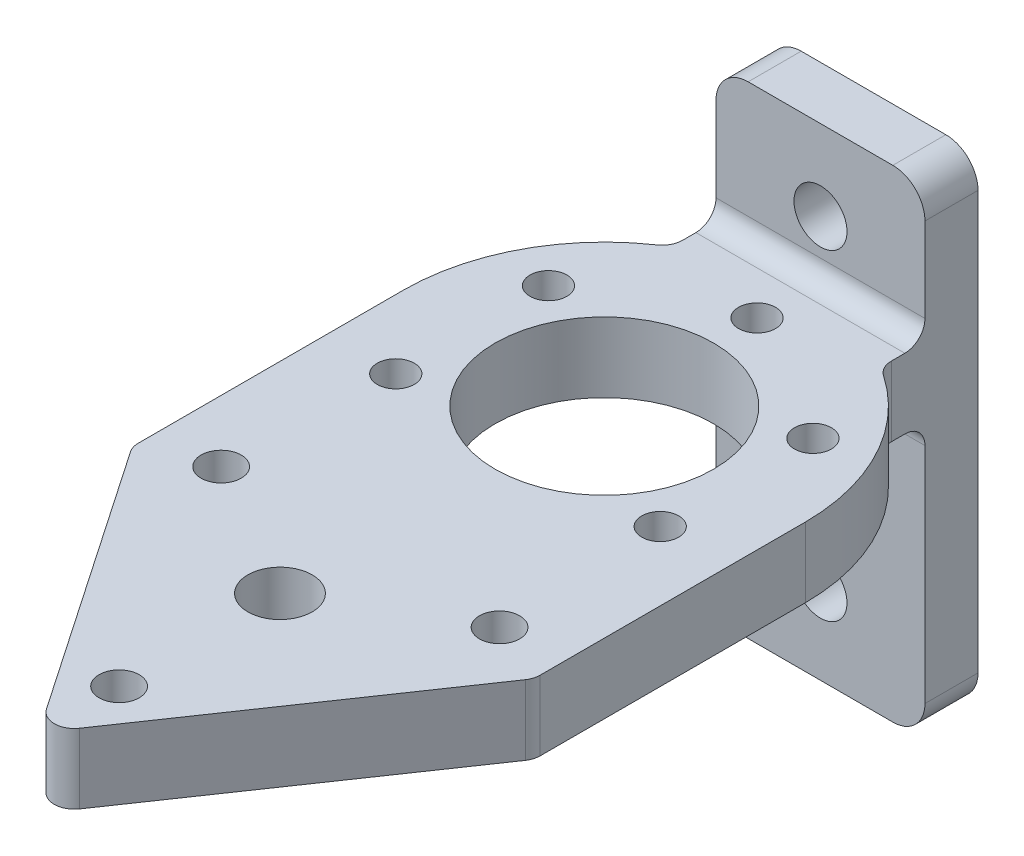
SolidWorks part; units mm, degrees
material "PLA"
ref_plane "Plan de face" through (0, 0, 0) normal (0, 0, 1) x (1, 0, 0)
ref_plane "Plan de dessus" through (0, 0, 0) normal (0, 1, 0) x (1, 0, 0)
ref_plane "Plan de droite" through (0, 0, 0) normal (1, 0, 0) x (0, 0, -1)
sketch "Esquisse1" plane through (0, 0, 0) normal (0, 0, 1) x (1, 0, 0)
  line L0 (55, 0) -> (-55, 0) construction
  line L1 (-6.5, -15) -> (6.5, -15)
  line L2 (-6.5, -15) -> (-6.5, 15)
  line L3 (-6.5, 15) -> (6.5, 15)
  line L4 (6.5, -15) -> (6.5, 15)
  line L5 (-6.5, -15) -> (6.5, 15) construction
  line L6 (-6.5, 15) -> (6.5, -15) construction
  circle A0 centre (0, 10) radius 1.65
  circle A1 centre (0, -10) radius 1.65
  point P0 (0, 0)
  dimension "D4" = 3.3
  dimension "D1" = 30
  dimension "D2" = 13
  dimension "D3" = 10
extrude "Boss.-Extru.1" add sketch "Esquisse1" along normal blind 3.3
fillet "Congé1" radius 2 4 edges at (6.5, -15, 1.65) (-6.5, -15, 1.65) (6.5, 15, 1.65) (-6.5, 15, 1.65)
sketch "Esquisse2" plane through (0, 0, 3.3) normal (0, 0, 1) x (1, 0, 0)
  line L0 (6.5, -13) -> (6.5, 13) construction
  line L3 (-6.5, 6.5) -> (6.5, 6.5)
  line L5 (-6.5, 13) -> (-6.5, -13) construction
  line L7 (-6.5, 6.5) -> (-6.5, 2.15)
  line L10 (-6.5, 2.15) -> (6.5, 2.15)
  line L14 (6.5, 6.5) -> (6.5, 2.15)
  point P0 (0, 0)
  point P8 (0, 0)
  dimension "D1" = 2.15
  dimension "D3" = 4.35
extrude "Boss.-Extru.2" add sketch "Esquisse2" along normal blind 2.77
sketch "Esquisse4" plane through (0, 6.5, 0) normal (0, 1, 0) x (1, 0, 0)
  line L1 (-6.5, -6.07) -> (6.5, -6.07)
  line L3 (-6.5, -27.4242) -> (6.5, -27.4242)
  circle A4 centre (0, -16.7471) radius 6.8
  arc A5 (-6.5, -6.07) -> (-6.5, -27.4242) centre (0, -16.7471) ccw
  arc A6 (6.5, -27.4242) -> (6.5, -6.07) centre (0, -16.7471) ccw
  point P25 (0, -16.7471)
  point P28 (0, -16.7471)
  dimension "D2" = 12.5
  dimension "D3" = 13
  dimension "D6" = 13.6
  dimension "D1" = 12.5
extrude "Boss.-Extru.4" add sketch "Esquisse4" against normal up to surface (4.35 mm away) up to face at (0, 2.15, 4.685)
sketch "Esquisse6" plane through (0, 6.5, 0) normal (0, 1, 0) x (1, 0, 0)
  line L2 (0, -16.7471) -> (8.2272, -11.9971) construction
  line L3 (0, -16.7471) -> (-8.2272, -11.9971) construction
  line L4 (0, -16.7471) -> (0, -7.2471) construction
  line L5 (0, -16.7471) -> (-8.2272, -21.4971) construction
  line L6 (0, -16.7471) -> (0, -26.2471) construction
  line L7 (0, -16.7471) -> (8.2272, -21.4971) construction
  circle A0 centre (0, -7.2471) radius 1.15
  circle A1 centre (-8.2272, -11.9971) radius 1.15
  circle A2 centre (8.2272, -11.9971) radius 1.15
  circle A3 centre (-8.2272, -21.4971) radius 1.15
  circle A7 centre (8.2272, -21.4971) radius 1.15
  dimension "D2" = 2.3
  dimension "D5" = 2.3
  dimension "D6" = 2.3
  dimension "D7" = 9.5
  dimension "D14" = 2.3
  dimension "D15" = 2.3
  dimension "D1" = 9.5
  dimension "D3" = 60
  dimension "D4" = 60
  dimension "D8" = 9.5
  dimension "D9" = 60
  dimension "D10" = 60
  dimension "D11" = 9.5
  dimension "D12" = 9.5
  dimension "D13" = 9.5
extrude "Enlèv. mat.-Extru.2" cut sketch "Esquisse6" against normal through all
sketch "Esquisse8" plane through (0, 6.5, 0) normal (0, 1, 0) x (1, 0, 0)
  line L6 (-6.5, -27.4242) -> (6.5, -27.4242) construction
  line L8 (0, -9.9471) -> (0, -23.5471) construction
  line L9 (0, -36.9271) -> (0, -27.4242) construction
  line L10 (0, -36.9271) -> (8.6603, -31.9271) construction
  line L11 (0, -36.9271) -> (-8.6603, -31.9271) construction
  line L16 (12.5, -16.7471) -> (12.5, -33.6271) construction
  line L17 (-12.5, -16.7471) -> (-12.5, -33.6258) construction
  line L18 (0, -51.9371) -> (-12.5, -33.6258)
  line L19 (-12.5, -33.6258) -> (-12.5, -16.7471)
  line L20 (0, -51.9371) -> (12.5, -33.6271)
  line L21 (12.5, -33.6271) -> (12.5, -16.7471)
  line L22 (-6.5, -27.4242) -> (6.5, -27.4242)
  circle A0 centre (0, -36.9271) radius 2
  circle A1 centre (0, -36.9271) radius 10 construction
  circle A2 centre (8.6603, -31.9271) radius 1.25
  circle A3 centre (0, -16.7471) radius 6.8 construction
  circle A4 centre (-8.6603, -31.9271) radius 1.25
  circle A7 centre (0, -46.9371) radius 1.25
  arc A8 (6.5, -27.4242) -> (6.5, -6.07) centre (0, -16.7471) ccw construction
  arc A9 (-6.5, -6.07) -> (-6.5, -27.4242) centre (0, -16.7471) ccw construction
  arc A11 (-12.5, -16.7471) -> (-6.5, -27.4242) centre (0, -16.7471) ccw
  arc A12 (12.5, -16.7471) -> (6.5, -27.4242) centre (0, -16.7471) cw
  point P16 (0, -16.7471)
  dimension "D2" = 4
  dimension "D5" = 2.5
  dimension "D6" = 2.5
  dimension "D7" = 2.5
  dimension "D12" = 10.01
  dimension "D1" = 20.18
  dimension "D3" = 120
  dimension "D4" = 60
  dimension "D8" = 16.8787
  dimension "D9" = 16.88
  dimension "D10" = 5
  dimension "D11" = 8.6603
extrude "Boss.-Extru.5" add sketch "Esquisse8" against normal up to surface (4.35 mm away) up to face at (0, 2.15, 8.3971)
fillet "Congé2" radius 1.25 7 edges at (12.5, 4.325, 33.6271) (-12.5, 4.325, 33.6258) (0, 4.325, 51.9371) (0, 2.15, 3.3) (0, 6.5, 3.3) (6.5, 4.325, 6.07) (-6.5, 4.325, 6.07)
